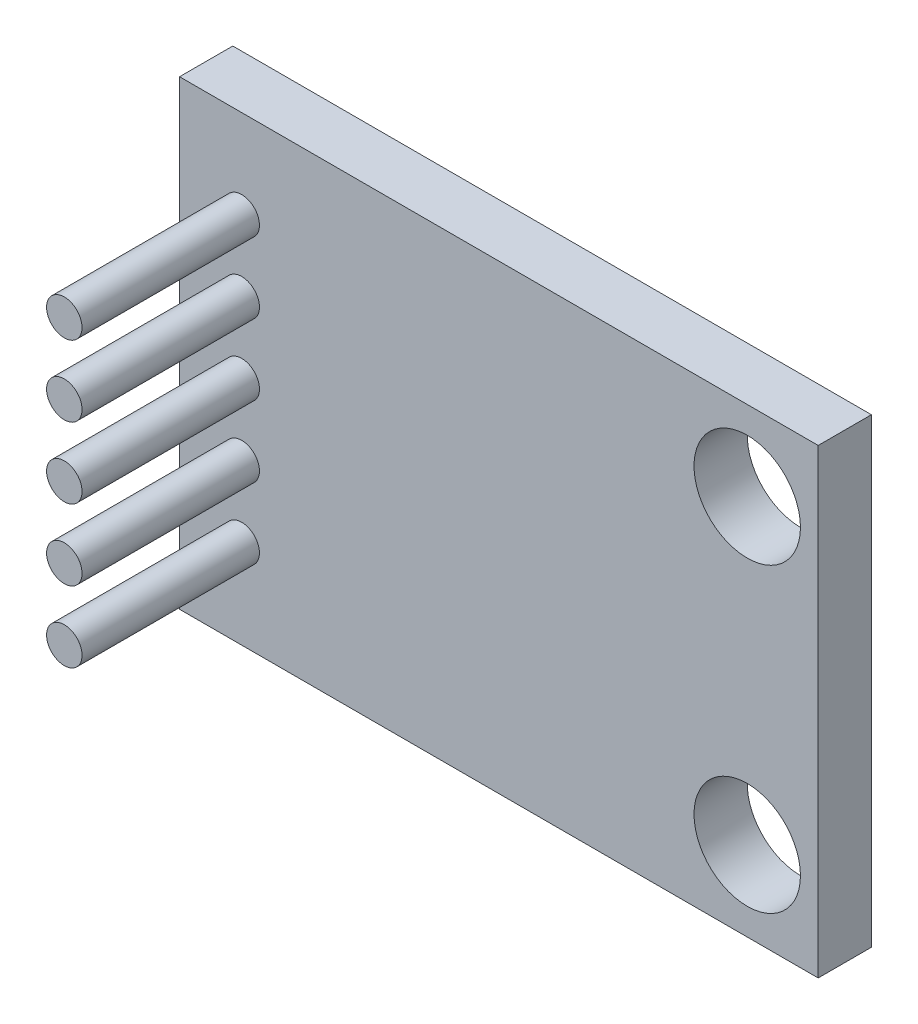
SolidWorks part; units mm, degrees
ref_plane "Front Plane" through (0, 0, 0) normal (0, 0, 1) x (1, 0, 0)
ref_plane "Top Plane" through (0, 0, 0) normal (0, 1, 0) x (1, 0, 0)
ref_plane "Right Plane" through (0, 0, 0) normal (1, 0, 0) x (0, 0, -1)
sketch "Sketch1" plane through (0, 0, 0) normal (0, 0, 1) x (1, 0, 0)
  line L1 (156.5831, 59.8072) -> (174.5831, 59.8072)
  line L2 (156.5831, 59.8072) -> (156.5831, 46.8072)
  line L3 (156.5831, 46.8072) -> (174.5831, 46.8072)
  line L4 (174.5831, 59.8072) -> (174.5831, 46.8072)
extrude "Boss-Extrude1" add sketch "Sketch1" along normal blind 1.5
sketch "Sketch2" plane through (0, 0, 1.5) normal (0, 0, 1) x (1, 0, 0)
  line L0 (156.5831, 53.3072) -> (174.5831, 53.3072) construction
  line L1 (156.5831, 59.8072) -> (156.5831, 46.8072) construction
  line L2 (174.5831, 46.8072) -> (174.5831, 59.8072) construction
  circle A0 centre (158.3342, 53.3072) radius 0.5
  circle A2 centre (158.3342, 55.3072) radius 0.5
  circle A3 centre (158.3342, 57.3072) radius 0.5
  circle A7 centre (158.3342, 51.3072) radius 0.5
  circle A8 centre (158.3342, 49.3072) radius 0.5
  circle A9 centre (168.3342, 53.3072) radius 0.5 [skipped]
  circle A10 centre (168.3342, 51.3072) radius 0.5 [skipped]
  circle A11 centre (168.3342, 49.3072) radius 0.5 [skipped]
  dimension "D1" = 3
  dimension "D2" = 2
  dimension "D3" = 3
extrude "Boss-Extrude2" add sketch "Sketch2" along normal blind 5
sketch "Sketch3" plane through (0, 0, 1.5) normal (0, 0, 1) x (1, 0, 0)
  line L0 (174.5831, 53.3072) -> (156.5831, 53.3072) construction
  line L1 (174.5831, 46.8072) -> (174.5831, 59.8072) construction
  line L2 (156.5831, 59.8072) -> (156.5831, 46.8072) construction
  circle A0 centre (172.5831, 57.5572) radius 1.5
  circle A2 centre (172.5831, 49.0572) radius 1.5
extrude "Cut-Extrude1" cut sketch "Sketch3" against normal up to surface (3.5 mm away)
